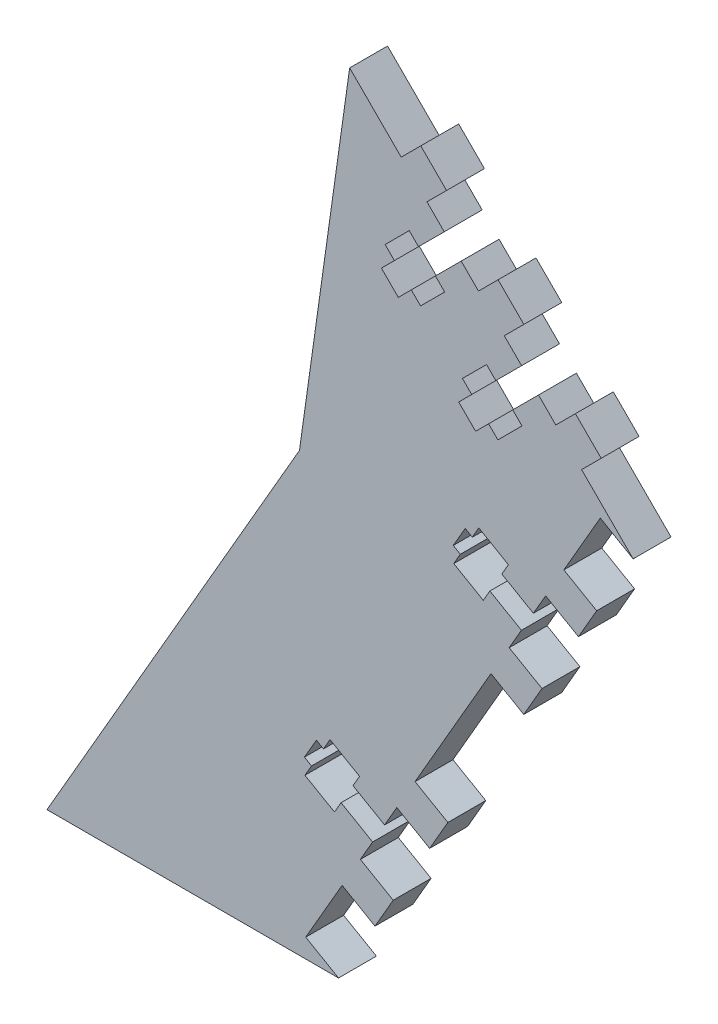
SolidWorks part; units mm, degrees
material "Acrylic (Blue)"
ref_plane "Front Plane" through (0, 0, 0) normal (0, 0, 1) x (1, 0, 0)
ref_plane "Top Plane" through (0, 0, 0) normal (0, 1, 0) x (1, 0, 0)
ref_plane "Right Plane" through (0, 0, 0) normal (1, 0, 0) x (0, 0, -1)
sketch "Sketch1" plane through (0, 0, 0) normal (0, 0, 1) x (1, 0, 0)
  line L0 (0, 0) -> (0, 304.4261) construction
  line L1 (0, 304.4261) -> (215.5261, 88.9)
  line L2 (215.5261, 88.9) -> (164.1997, 0)
  line L3 (164.1997, 0) -> (0, 0)
  line L4 (0, 304.4261) -> (-215.5261, 88.9)
  line L5 (-215.5261, 88.9) -> (-164.1997, 0)
  line L6 (-164.1997, 0) -> (0, 0)
  line L7 (-215.5261, 88.9) -> (215.5261, 88.9) construction
  line L8 (0, 304.4261) -> (3.5921, 308.0182) construction
  line L9 (3.5921, 308.0182) -> (219.1182, 92.4921) construction
  line L10 (219.1182, 92.4921) -> (215.5261, 88.9) construction
  line L11 (3.5921, 308.0182) -> (0, 311.6104) construction
  line L12 (0, 311.6104) -> (-219.1182, 92.4921) construction
  line L13 (-219.1182, 92.4921) -> (-215.5261, 88.9) construction
  line L14 (215.5261, 88.9) -> (219.9256, 86.36) construction
  line L15 (219.9256, 86.36) -> (168.5991, -2.54) construction
  line L16 (168.5991, -2.54) -> (164.1997, 0) construction
  line L17 (164.1997, 0) -> (164.1997, -12.7) construction
  line L18 (164.1997, -12.7) -> (-164.1997, -12.7) construction
  line L19 (-164.1997, -12.7) -> (-164.1997, 0) construction
  line L20 (-164.1997, 0) -> (-168.5991, -2.54) construction
  line L21 (-168.5991, -2.54) -> (-219.9256, 86.36) construction
  line L22 (-219.9256, 86.36) -> (-215.5261, 88.9) construction
  dimension "D1" = 304.8
  dimension "D2" = 120
  dimension "D3" = 88.9
  dimension "D4" = 5.08
  dimension "D5" = 12.7
extrude "Boss-Extrude1" add sketch "Sketch1" along normal blind 6.604
other "Move Face2" face at (107.7631, 196.6631, 3.302) parameters "D1"=0.0025
sketch "Sketch2" plane through (0, 0, 6.604) normal (0, 0, 1) x (1, 0, 0)
  line L1 (113.3997, 0) -> (157.3938, 76.2)
  line L2 (-164.1997, 0) -> (164.1997, 0) construction
  line L3 (157.3938, 76.2) -> (166.1361, 138.2937)
  line L4 (215.5275, 88.9023) -> (0.0018, 304.4279) construction
  line L5 (164.1997, 0) -> (215.5275, 88.9023) construction
  line L7 (166.1361, 138.2937) -> (0.0018, 304.4279)
  line L9 (0.0018, 304.4279) -> (-215.5261, 88.9)
  line L10 (-215.5261, 88.9) -> (-164.1997, 0)
  line L11 (-164.1997, 0) -> (113.3997, 0)
  line B0 (185.1383, 97.3796) -> (188.0838, 94.4341) construction
  dimension "D1" = 50.8
  dimension "D2" = 12.7
  dimension "D3" = 76.2
  dimension "D4" = 12.7
sketch_block_instance "NUT_HOLE_2X-1"
sketch_block "NUT_HOLE_2X" parameters "D1"=6.35, "D2"=4.1656, "D3"=25.4, "D4"=4.826, "D5"=8.7376, "D6"=5.9436, "D7"=6.35, "D8"=20.32, "D9"=2
extrude "Cut-Extrude1" cut sketch "Sketch2" against normal through all
sketch "Sketch3" plane through (0, 0, 6.604) normal (0, 0, 1) x (1, 0, 0)
  line L0 (164.1997, 0) -> (215.5275, 88.9023) construction
  line L5 (158.4805, 3.302) -> (209.8069, 92.202)
  line L6 (164.1997, 0) -> (158.4805, 3.302)
  line L7 (215.5261, 88.9) -> (164.1997, 0)
  line L8 (209.8069, 92.202) -> (215.5261, 88.9)
  dimension "D1" = 6.604
  dimension "D2" = 102.6529
extrude "Cut-Extrude2" cut sketch "Sketch3" against normal through all
sketch "Sketch4" plane through (0, 0, 6.604) normal (0, 0, 1) x (1, 0, 0)
  line L0 (215.5275, 88.9023) -> (166.1361, 138.2937) construction
  line L1 (209.8069, 92.202) -> (158.4805, 3.302) construction
  line L2 (215.5261, 88.9) -> (209.8069, 92.202) construction
  point P9 (212.6665, 90.551)
  line B0 (198.1483, 72.0087) -> (192.6491, 75.1837) construction
  line B1 (192.6491, 75.1837) -> (193.7921, 77.1634) construction
  line B2 (193.7921, 77.1634) -> (188.6447, 80.1352) construction
  line B3 (188.6447, 80.1352) -> (187.5017, 78.1555) construction
  line B4 (187.5017, 78.1555) -> (186.2699, 78.8667) construction
  line B5 (186.2699, 78.8667) -> (184.1871, 75.2592) construction
  line B6 (184.1871, 75.2592) -> (185.4189, 74.548) construction
  line B7 (185.4189, 74.548) -> (184.2759, 72.5683) construction
  line B8 (184.2759, 72.5683) -> (189.4233, 69.5965) construction
  line B9 (189.4233, 69.5965) -> (190.5663, 71.5762) construction
  line B10 (190.5663, 71.5762) -> (196.0655, 68.4012) construction
  line B11 (196.0655, 68.4012) -> (193.9319, 64.7057) construction
  line B12 (193.9319, 64.7057) -> (199.6511, 61.4037) construction
  line B13 (199.6511, 61.4037) -> (196.4761, 55.9044) construction
  line B14 (196.4761, 55.9044) -> (190.7569, 59.2064) construction
  line B15 (198.1483, 72.0087) -> (200.2819, 75.7042) construction
  line B16 (200.2819, 75.7042) -> (206.0011, 72.4022) construction
  line B17 (206.0011, 72.4022) -> (209.1761, 77.9015) construction
  line B18 (209.1761, 77.9015) -> (203.4569, 81.2035) construction
  line B19 (196.0655, 68.4012) -> (198.1483, 72.0087) construction
  line B20 (172.2219, 27.1028) -> (166.7226, 30.2778) construction
  line B21 (166.7226, 30.2778) -> (167.8656, 32.2575) construction
  line B22 (167.8656, 32.2575) -> (162.7183, 35.2293) construction
  line B23 (162.7183, 35.2293) -> (161.5753, 33.2496) construction
  line B24 (161.5753, 33.2496) -> (160.3435, 33.9608) construction
  line B25 (160.3435, 33.9608) -> (158.2607, 30.3533) construction
  line B26 (158.2607, 30.3533) -> (159.4925, 29.6421) construction
  line B27 (159.4925, 29.6421) -> (158.3495, 27.6624) construction
  line B28 (158.3495, 27.6624) -> (163.4968, 24.6906) construction
  line B29 (163.4968, 24.6906) -> (164.6398, 26.6703) construction
  line B30 (164.6398, 26.6703) -> (170.1391, 23.4953) construction
  line B31 (170.1391, 23.4953) -> (168.0055, 19.7998) construction
  line B32 (168.0055, 19.7998) -> (173.7247, 16.4978) construction
  line B33 (173.7247, 16.4978) -> (170.5497, 10.9985) construction
  line B34 (170.5497, 10.9985) -> (164.8305, 14.3005) construction
  line B35 (172.2219, 27.1028) -> (174.3555, 30.7983) construction
  line B36 (174.3555, 30.7983) -> (180.0747, 27.4963) construction
  line B37 (180.0747, 27.4963) -> (183.2497, 32.9956) construction
  line B38 (183.2497, 32.9956) -> (177.5305, 36.2976) construction
  line B39 (170.1391, 23.4953) -> (172.2219, 27.1028) construction
  line B40 (182.6238, 121.8059) -> (178.1337, 117.3158) construction
  line B41 (178.1337, 117.3158) -> (176.5172, 118.9323) construction
  line B42 (176.5172, 118.9323) -> (172.3145, 114.7295) construction
  line B43 (172.3145, 114.7295) -> (173.9309, 113.113) construction
  line B44 (173.9309, 113.113) -> (171.6679, 110.85) construction
  line B45 (171.6679, 110.85) -> (174.6134, 107.9045) construction
  line B46 (174.6134, 107.9045) -> (176.8764, 110.1675) construction
  line B47 (176.8764, 110.1675) -> (178.4929, 108.5511) construction
  line B48 (178.4929, 108.5511) -> (182.6956, 112.7538) construction
  line B49 (182.6956, 112.7538) -> (181.0792, 114.3703) construction
  line B50 (181.0792, 114.3703) -> (185.5693, 118.8604) construction
  line B51 (185.5693, 118.8604) -> (188.5867, 115.843) construction
  line B52 (188.5867, 115.843) -> (191.9992, 119.2555) construction
  line B53 (191.9992, 119.2555) -> (196.4893, 114.7654) construction
  line B54 (196.4893, 114.7654) -> (193.0768, 111.3529) construction
  line B55 (182.6238, 121.8059) -> (179.6064, 124.8233) construction
  line B56 (179.6064, 124.8233) -> (183.0189, 128.2358) construction
  line B57 (183.0189, 128.2358) -> (178.5288, 132.7259) construction
  line B58 (178.5288, 132.7259) -> (175.1163, 129.3134) construction
  line B59 (209.9597, 101.295) -> (206.5472, 97.8825) construction
  line B60 (196.0942, 108.3356) -> (191.6041, 103.8454) construction
  line B61 (191.6041, 103.8454) -> (189.9876, 105.4619) construction
  line B62 (189.9876, 105.4619) -> (185.7849, 101.2591) construction
  line B63 (185.7849, 101.2591) -> (187.4013, 99.6427) construction
  line B64 (187.4013, 99.6427) -> (185.1383, 97.3796) construction
  line B65 (185.1383, 97.3796) -> (188.0838, 94.4341) construction
  line B66 (188.0838, 94.4341) -> (190.3468, 96.6971) construction
  line B67 (190.3468, 96.6971) -> (191.9633, 95.0807) construction
  line B68 (191.9633, 95.0807) -> (196.166, 99.2835) construction
  line B69 (196.166, 99.2835) -> (194.5496, 100.8999) construction
  line B70 (194.5496, 100.8999) -> (199.0397, 105.39) construction
  line B71 (199.0397, 105.39) -> (202.0571, 102.3727) construction
  line B72 (202.0571, 102.3727) -> (205.4696, 105.7852) construction
  line B73 (205.4696, 105.7852) -> (209.9597, 101.295) construction
  line B74 (196.0942, 108.3356) -> (193.0768, 111.3529) construction
  line B75 (199.0397, 105.39) -> (196.0942, 108.3356) construction
  dimension "D1" = 12.7
  dimension "D2" = 12.7
  dimension "D3" = 12.7
sketch_block_instance "NUT_HOLE-21"
sketch_block "NUT_HOLE" parameters "D1"=6.35, "D2"=4.1656, "D3"=25.4, "D4"=6.604, "D5"=8.7376, "D6"=5.9436, "D7"=6.35, "D8"=20.32
sketch_block_instance "NUT_HOLE-22"
sketch_block_instance "NUT_HOLE_2X-3"
sketch "Sketch5" plane through (0, 0, 6.604) normal (0, 0, 1) x (1, 0, 0)
  line L0 (182.6238, 121.8059) -> (178.1337, 117.3158) construction
  line L1 (176.5172, 118.9323) -> (172.3145, 114.7295) construction
  line L2 (172.3145, 114.7295) -> (173.9309, 113.113) construction
  line L3 (173.9309, 113.113) -> (171.6679, 110.85) construction
  line L4 (171.6679, 110.85) -> (174.6134, 107.9045) construction
  line L5 (174.6134, 107.9045) -> (176.8764, 110.1675) construction
  line L6 (176.8764, 110.1675) -> (178.4929, 108.5511) construction
  line L7 (178.4929, 108.5511) -> (182.6956, 112.7538) construction
  line L8 (181.0792, 114.3703) -> (185.5693, 118.8604) construction
  line L9 (182.6956, 112.7538) -> (181.0792, 114.3703) construction
  line L10 (194.5496, 100.8999) -> (199.0397, 105.39) construction
  line L11 (196.0942, 108.3356) -> (191.6041, 103.8454) construction
  line L12 (191.6041, 103.8454) -> (189.9876, 105.4619) construction
  line L13 (189.9876, 105.4619) -> (185.7849, 101.2591) construction
  line L14 (185.7849, 101.2591) -> (187.4013, 99.6427) construction
  line L15 (187.4013, 99.6427) -> (185.1383, 97.3796) construction
  line L16 (185.1383, 97.3796) -> (188.0838, 94.4341) construction
  line L17 (188.0838, 94.4341) -> (190.3468, 96.6971) construction
  line L18 (190.3468, 96.6971) -> (191.9633, 95.0807) construction
  line L19 (191.9633, 95.0807) -> (196.166, 99.2835) construction
  line L20 (196.166, 99.2835) -> (194.5496, 100.8999) construction
  line L21 (182.6238, 121.8059) -> (178.1337, 117.3158)
  line L22 (176.5172, 118.9323) -> (172.3145, 114.7295)
  line L23 (172.3145, 114.7295) -> (173.9309, 113.113)
  line L24 (173.9309, 113.113) -> (171.6679, 110.85)
  line L25 (171.6679, 110.85) -> (174.6134, 107.9045)
  line L26 (174.6134, 107.9045) -> (176.8764, 110.1675)
  line L27 (176.8764, 110.1675) -> (178.4929, 108.5511)
  line L28 (178.4929, 108.5511) -> (182.6956, 112.7538)
  line L29 (181.0792, 114.3703) -> (185.5693, 118.8604)
  line L30 (182.6956, 112.7538) -> (181.0792, 114.3703)
  line L31 (194.5496, 100.8999) -> (199.0397, 105.39)
  line L32 (196.0942, 108.3356) -> (191.6041, 103.8454)
  line L33 (191.6041, 103.8454) -> (189.9876, 105.4619)
  line L34 (189.9876, 105.4619) -> (185.7849, 101.2591)
  line L35 (185.7849, 101.2591) -> (187.4013, 99.6427)
  line L36 (187.4013, 99.6427) -> (185.1383, 97.3796)
  line L37 (185.1383, 97.3796) -> (188.0838, 94.4341)
  line L38 (188.0838, 94.4341) -> (190.3468, 96.6971)
  line L39 (190.3468, 96.6971) -> (191.9633, 95.0807)
  line L40 (191.9633, 95.0807) -> (196.166, 99.2835)
  line L41 (196.166, 99.2835) -> (194.5496, 100.8999)
  line L42 (178.1337, 117.3158) -> (176.5172, 118.9323) construction
  line L43 (178.1337, 117.3158) -> (176.5172, 118.9323)
  line L44 (198.1483, 72.0087) -> (192.6491, 75.1837) construction
  line L45 (192.6491, 75.1837) -> (193.7921, 77.1634) construction
  line L46 (193.7921, 77.1634) -> (188.6447, 80.1352) construction
  line L47 (188.6447, 80.1352) -> (187.5017, 78.1555) construction
  line L48 (187.5017, 78.1555) -> (186.2699, 78.8667) construction
  line L49 (186.2699, 78.8667) -> (184.1871, 75.2592) construction
  line L50 (184.1871, 75.2592) -> (185.4189, 74.548) construction
  line L51 (185.4189, 74.548) -> (184.2759, 72.5683) construction
  line L52 (184.2759, 72.5683) -> (189.4233, 69.5965) construction
  line L53 (189.4233, 69.5965) -> (190.5663, 71.5762) construction
  line L54 (190.5663, 71.5762) -> (196.0655, 68.4012) construction
  line L55 (172.2219, 27.1028) -> (166.7226, 30.2778) construction
  line L56 (167.8656, 32.2575) -> (162.7183, 35.2293) construction
  line L57 (162.7183, 35.2293) -> (161.5753, 33.2496) construction
  line L58 (161.5753, 33.2496) -> (160.3435, 33.9608) construction
  line L59 (160.3435, 33.9608) -> (158.2607, 30.3533) construction
  line L60 (158.2607, 30.3533) -> (159.4925, 29.6421) construction
  line L61 (159.4925, 29.6421) -> (158.3495, 27.6624) construction
  line L62 (158.3495, 27.6624) -> (163.4968, 24.6906) construction
  line L63 (163.4968, 24.6906) -> (164.6398, 26.6703) construction
  line L64 (164.6398, 26.6703) -> (170.1391, 23.4953) construction
  line L65 (166.7226, 30.2778) -> (167.8656, 32.2575) construction
  line L66 (198.1483, 72.0087) -> (192.6491, 75.1837)
  line L67 (192.6491, 75.1837) -> (193.7921, 77.1634)
  line L68 (193.7921, 77.1634) -> (188.6447, 80.1352)
  line L69 (188.6447, 80.1352) -> (187.5017, 78.1555)
  line L70 (187.5017, 78.1555) -> (186.2699, 78.8667)
  line L71 (186.2699, 78.8667) -> (184.1871, 75.2592)
  line L72 (184.1871, 75.2592) -> (185.4189, 74.548)
  line L73 (185.4189, 74.548) -> (184.2759, 72.5683)
  line L74 (184.2759, 72.5683) -> (189.4233, 69.5965)
  line L75 (189.4233, 69.5965) -> (190.5663, 71.5762)
  line L76 (190.5663, 71.5762) -> (196.0655, 68.4012)
  line L77 (172.2219, 27.1028) -> (166.7226, 30.2778)
  line L78 (167.8656, 32.2575) -> (162.7183, 35.2293)
  line L79 (162.7183, 35.2293) -> (161.5753, 33.2496)
  line L80 (161.5753, 33.2496) -> (160.3435, 33.9608)
  line L81 (160.3435, 33.9608) -> (158.2607, 30.3533)
  line L82 (158.2607, 30.3533) -> (159.4925, 29.6421)
  line L83 (159.4925, 29.6421) -> (158.3495, 27.6624)
  line L84 (158.3495, 27.6624) -> (163.4968, 24.6906)
  line L85 (163.4968, 24.6906) -> (164.6398, 26.6703)
  line L86 (164.6398, 26.6703) -> (170.1391, 23.4953)
  line L87 (166.7226, 30.2778) -> (167.8656, 32.2575)
  line L88 (170.1391, 23.4953) -> (172.2219, 27.1028)
  line L89 (198.1483, 72.0087) -> (196.0655, 68.4012)
  line L90 (182.6238, 121.8059) -> (185.5693, 118.8604)
  line L91 (196.0942, 108.3356) -> (199.0397, 105.39)
  point P0 (176.5172, 118.9323)
extrude "Cut-Extrude3" cut sketch "Sketch5" against normal through all
sketch "Sketch6" plane through (0, 0, 6.604) normal (0, 0, 1) x (1, 0, 0)
  line L0 (178.5288, 132.7259) -> (175.1163, 129.3134) construction
  line L1 (179.6064, 124.8233) -> (183.0189, 128.2358) construction
  line L2 (183.0189, 128.2358) -> (178.5288, 132.7259) construction
  line L3 (188.5867, 115.843) -> (191.9992, 119.2555) construction
  line L4 (191.9992, 119.2555) -> (196.4893, 114.7654) construction
  line L5 (196.4893, 114.7654) -> (193.0768, 111.3529) construction
  line L6 (205.4696, 105.7852) -> (209.9597, 101.295) construction
  line L7 (202.0571, 102.3727) -> (205.4696, 105.7852) construction
  line L8 (209.9597, 101.295) -> (206.5472, 97.8825) construction
  line L9 (178.5288, 132.7259) -> (175.1163, 129.3134)
  line L10 (179.6064, 124.8233) -> (183.0189, 128.2358)
  line L11 (183.0189, 128.2358) -> (178.5288, 132.7259)
  line L12 (188.5867, 115.843) -> (191.9992, 119.2555)
  line L13 (191.9992, 119.2555) -> (196.4893, 114.7654)
  line L14 (196.4893, 114.7654) -> (193.0768, 111.3529)
  line L15 (205.4696, 105.7852) -> (209.9597, 101.295)
  line L16 (202.0571, 102.3727) -> (205.4696, 105.7852)
  line L17 (209.9597, 101.295) -> (206.5472, 97.8825)
  line L27 (209.1761, 77.9015) -> (203.4569, 81.2035) construction
  line L28 (206.0011, 72.4022) -> (209.1761, 77.9015) construction
  line L29 (200.2819, 75.7042) -> (206.0011, 72.4022) construction
  line L30 (193.9319, 64.7057) -> (199.6511, 61.4037) construction
  line L31 (199.6511, 61.4037) -> (196.4761, 55.9044) construction
  line L32 (196.4761, 55.9044) -> (190.7569, 59.2064) construction
  line L33 (183.2497, 32.9956) -> (177.5305, 36.2976) construction
  line L34 (180.0747, 27.4963) -> (183.2497, 32.9956) construction
  line L35 (174.3555, 30.7983) -> (180.0747, 27.4963) construction
  line L36 (168.0055, 19.7998) -> (173.7247, 16.4978) construction
  line L37 (173.7247, 16.4978) -> (170.5497, 10.9985) construction
  line L38 (170.5497, 10.9985) -> (164.8305, 14.3005) construction
  line L39 (209.1761, 77.9015) -> (203.4569, 81.2035)
  line L40 (206.0011, 72.4022) -> (209.1761, 77.9015)
  line L41 (200.2819, 75.7042) -> (206.0011, 72.4022)
  line L42 (175.1163, 129.3134) -> (179.6064, 124.8233)
  line L43 (188.5867, 115.843) -> (193.0768, 111.3529)
  line L44 (202.0571, 102.3727) -> (206.5472, 97.8825)
  line L45 (203.4569, 81.2035) -> (200.2819, 75.7042)
  line L46 (193.9319, 64.7057) -> (199.6511, 61.4037)
  line L47 (199.6511, 61.4037) -> (196.4761, 55.9044)
  line L48 (196.4761, 55.9044) -> (190.7569, 59.2064)
  line L49 (183.2497, 32.9956) -> (177.5305, 36.2976)
  line L50 (180.0747, 27.4963) -> (183.2497, 32.9956)
  line L51 (174.3555, 30.7983) -> (180.0747, 27.4963)
  line L52 (168.0055, 19.7998) -> (173.7247, 16.4978)
  line L53 (173.7247, 16.4978) -> (170.5497, 10.9985)
  line L54 (170.5497, 10.9985) -> (164.8305, 14.3005)
  line L55 (164.8305, 14.3005) -> (168.0055, 19.7998)
  line L56 (174.3555, 30.7983) -> (177.5305, 36.2976)
  line L57 (190.7569, 59.2064) -> (193.9319, 64.7057)
extrude "Boss-Extrude2" add sketch "Sketch6" against normal up to surface (6.604 mm away) up to face at (179.8913, 77.0164, 0)
other "Move Face3" [suppressed] parameters "D1"=0.0508
